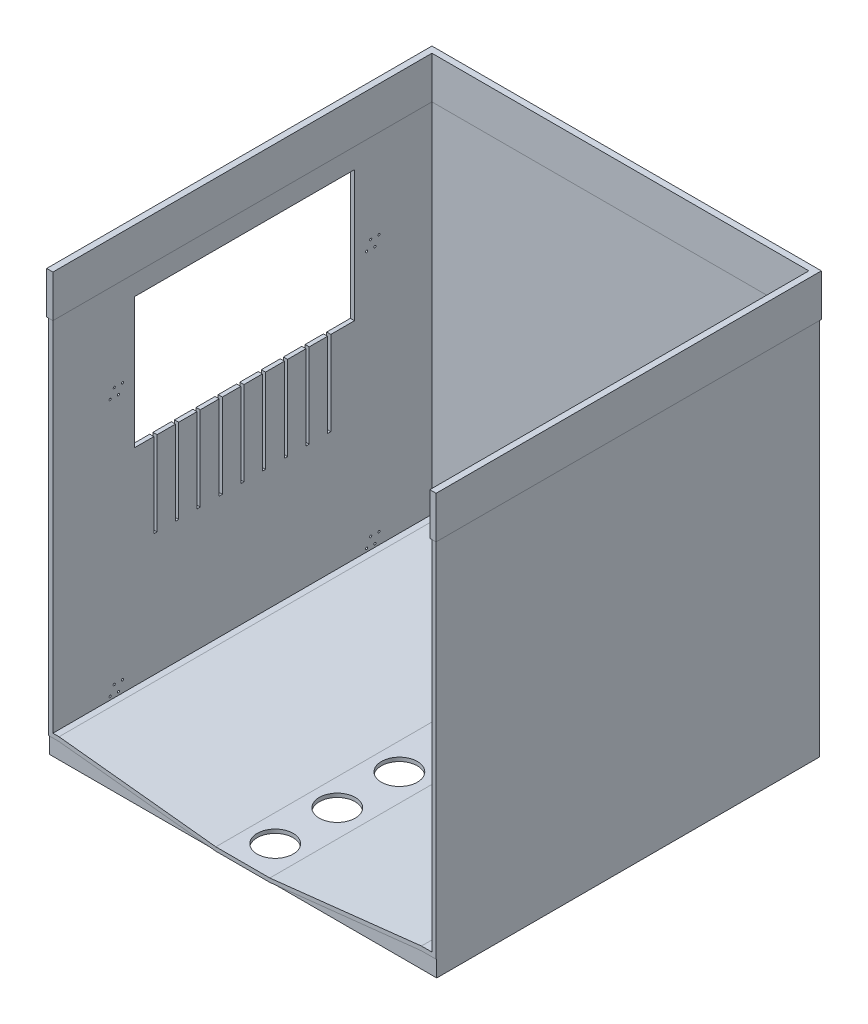
SolidWorks part; units mm, degrees
other "Markup1"
sketch "Sketch7" plane through (469.7075, 914.4, 622.6947) normal (0.575, 0.8073, 0.133) x (0.2253, 0, -0.9743)
ref_plane "Front Plane" through (0, 0, 0) normal (0, 0, 1) x (1, 0, 0)
ref_plane "Top Plane" through (0, 0, 0) normal (0, 1, 0) x (1, 0, 0)
ref_plane "Right Plane" through (0, 0, 0) normal (1, 0, 0) x (0, 0, -1)
sketch "Sketch1" plane through (0, 0, 0) normal (0, 1, 0) x (1, 0, 0)
  line L1 (-454.6925, 291.7053) -> (459.7075, 291.7053)
  line L2 (-454.6925, 291.7053) -> (-454.6925, -622.6947)
  line L3 (-454.6925, -622.6947) -> (459.7075, -622.6947)
  line L4 (459.7075, 291.7053) -> (459.7075, -622.6947)
  dimension "D1" = 914.4
  dimension "D2" = 914.4
extrude "Boss-Extrude1" add sketch "Sketch1" along normal blind 50
sketch "Sketch2" plane through (459.7075, 0, 0) normal (1, 0, 0) x (0, 0, -1)
  line L0 (291.7053, 50) -> (291.7053, 0) construction
  line L1 (-622.6947, 0) -> (291.7053, 0)
  line L2 (-622.6947, 0) -> (-622.6947, 914.4)
  line L3 (-622.6947, 914.4) -> (291.7053, 914.4)
  line L4 (291.7053, 0) -> (291.7053, 914.4)
  dimension "D1" = 914.4
  dimension "D2" = 0
extrude "Boss-Extrude2" add sketch "Sketch2" along normal blind 10
sketch "Sketch4" plane through (-454.6925, 0, 0) normal (-1, 0, 0) x (0, 0, 1)
  line L1 (-291.7053, 0) -> (622.6947, 0)
  line L2 (-291.7053, 0) -> (-291.7053, 914.4)
  line L3 (-291.7053, 914.4) -> (622.6947, 914.4)
  line L4 (622.6947, 0) -> (622.6947, 914.4)
extrude "Boss-Extrude3" add sketch "Sketch4" along normal blind 10
sketch "Sketch5" plane through (0, 0, -291.7053) normal (0, 0, -1) x (-1, 0, 0)
  line L0 (464.6925, 914.4) -> (464.6925, 0) construction
  line L1 (-469.7075, 0) -> (464.6925, 0)
  line L2 (-469.7075, 0) -> (-469.7075, 914.4)
  line L3 (-469.7075, 914.4) -> (464.6925, 914.4)
  line L4 (464.6925, 0) -> (464.6925, 914.4)
extrude "Boss-Extrude4" add sketch "Sketch5" along normal blind 10 contours L3 L4 L1 L2
sketch "Sketch6" plane through (0, 0, 622.6947) normal (0, 0, 1) x (1, 0, 0)
  line L0 (0, 0) -> (-61.619, 0)
  line L1 (-464.6925, 0) -> (469.7075, 0) construction
  line L2 (0, 0) -> (68.6447, 0)
  line L3 (68.6447, 0) -> (434.3849, 40)
  line L4 (434.3849, 40) -> (469.7075, 40)
  line L5 (469.7075, 914.4) -> (469.7075, 0) construction
  line L6 (-61.619, 0) -> (-439.8845, 40)
  line L7 (-439.8845, 40) -> (-464.6925, 40)
  line L8 (-464.6925, 0) -> (-464.6925, 914.4) construction
  line L9 (469.7075, 40) -> (469.7075, 0)
  line L10 (469.7075, 0) -> (68.6447, 0)
  line L11 (-464.6925, 40) -> (-464.6925, 0)
  line L12 (-464.6925, 0) -> (-61.619, 0)
  line L13 (459.7075, 50) -> (-454.6925, 50) construction
  line L14 (-439.8845, 50) -> (-61.619, 9.2201)
  line L15 (-454.6925, 50) -> (459.7075, 50) construction
  line L16 (-61.619, 9.2201) -> (-61.619, 0)
  line L17 (-439.8845, 50) -> (434.3849, 50)
  line L18 (434.3849, 50) -> (68.6447, 9.2201)
  line L19 (68.6447, 9.2201) -> (-61.619, 9.2201)
  line L20 (68.6447, 0) -> (68.6447, 9.2201)
  line L21 (434.3849, 40) -> (434.3849, 50)
  line M13 (-464.6925, 0) -> (469.7075, 0)
  line M14 (469.7075, 0) -> (469.7075, 914.4)
  line M17 (459.7075, 50) -> (-454.6925, 50)
  line M20 (-464.6925, 914.4) -> (-464.6925, 0)
  dimension "D1" = 10
  dimension "D2" = 10
  dimension "D3" = 35.3226
  dimension "D4" = 378.2656
  dimension "D5" = 378.2656
extrude "Cut-Extrude2" cut sketch "Sketch6" against normal through all contours L6 L7 M20 M13 | L19 L18 L14 M17 | L4 L3 M13 M14
sketch "Sketch8" plane through (0, 0, -301.7053) normal (0, 0, -1) x (-1, 0, 0)
  line L0 (-434.3849, 50) -> (-68.6447, 9.2201)
  line L1 (-68.6447, 9.2201) -> (61.619, 9.2201)
  line L2 (61.619, 9.2201) -> (439.8845, 50)
  line L3 (439.8845, 50) -> (-434.3849, 50)
extrude "Boss-Extrude5" add sketch "Sketch8" against normal blind 10
sketch "Sketch10" plane through (0, 9.2201, 0) normal (0, 1, 0) x (1, 0, 0)
  line L0 (3.5129, -622.6947) -> (2.5075, 291.7053)
  line L1 (68.6447, -622.6947) -> (-61.619, -622.6947) construction
  line L2 (459.7075, 291.7053) -> (-454.6925, 291.7053) construction
  line L3 (3.427, -544.5816) -> (3.2621, -394.5816) construction
  circle A0 centre (3.427, -544.5816) radius 43.3569
  circle A1 centre (3.2621, -394.5816) radius 43.3569
  circle A2 centre (3.0971, -244.5817) radius 43.3569
  circle A3 centre (2.9322, -94.5818) radius 43.3569
  circle A4 centre (2.7673, 55.4181) radius 43.3569
  circle A5 centre (2.6024, 205.418) radius 43.3569
  dimension "D2" = 150
  dimension "D3" = 0
  dimension "D1" = 6
extrude "Cut-Extrude3" cut sketch "Sketch10" against normal through all contours A5 | A4 | A3 | A2 | A1 | A0
sketch "Sketch11" plane through (-464.6925, 0, 0) normal (-1, 0, 0) x (0, 0, 1)
  line L0 (-301.7053, 40) -> (622.6947, 40) construction
  line L1 (-104.8553, 863.6) -> (425.8447, 863.6)
  line L2 (-104.8553, 863.6) -> (-104.8553, 548)
  line L3 (-104.8553, 548) -> (425.8447, 548)
  line L4 (425.8447, 863.6) -> (425.8447, 548)
  line L5 (-301.7053, 40) -> (-301.7053, 914.4) construction
  line L6 (622.6947, 40) -> (622.6947, 914.4) construction
  line L7 (622.6947, 914.4) -> (-301.7053, 914.4) construction
  dimension "D1" = 508
  dimension "D2" = 196.85
  dimension "D3" = 196.85
  dimension "D4" = 50.8
extrude "Cut-Extrude4" cut sketch "Sketch11" against normal blind 10
sketch "Sketch14" plane through (0, 914.4, 0) normal (0, 1, 0) x (1, 0, 0)
  line L16 (457.1675, 289.1653) -> (457.1675, -625.2347)
  line L17 (457.1675, -625.2347) -> (472.2475, -625.2347)
  line L18 (472.2475, -625.2347) -> (472.2475, 304.2453)
  line L19 (472.2475, 304.2453) -> (-467.2325, 304.2453)
  line L20 (-467.2325, 304.2453) -> (-467.2325, -625.2347)
  line L21 (-467.2325, -625.2347) -> (-452.1525, -625.2347)
  line L22 (-452.1525, -625.2347) -> (-452.1525, 289.1653)
  line L23 (-452.1525, 289.1653) -> (457.1675, 289.1653)
  line L24 (457.1675, 289.1653) -> (457.1675, -625.2347)
  line L25 (457.1675, -625.2347) -> (472.2475, -625.2347)
  line L26 (472.2475, -625.2347) -> (472.2475, 304.2453)
  line L27 (472.2475, 304.2453) -> (-467.2325, 304.2453)
  line L28 (-467.2325, 304.2453) -> (-467.2325, -625.2347)
  line L29 (-467.2325, -625.2347) -> (-452.1525, -625.2347)
  line L30 (-452.1525, -625.2347) -> (-452.1525, 289.1653)
  line L31 (-452.1525, 289.1653) -> (457.1675, 289.1653)
  dimension "D1" = 2.54
extrude "Boss-Extrude7" add sketch "Sketch14" along normal blind 101.6
sketch "Sketch16" plane through (0, 0, -301.7053) normal (0, 0, -1) x (-1, 0, 0)
  line L0 (-469.7075, 40) -> (-469.7075, 0)
  line L1 (-469.7075, 0) -> (-68.6447, 0)
  line L2 (-68.6447, 0) -> (-434.3849, 40)
  line L3 (-434.3849, 40) -> (-469.7075, 40)
  line L4 (61.619, 0) -> (439.8845, 40)
  line L5 (439.8845, 40) -> (464.6925, 40)
  line L6 (464.6925, 40) -> (464.6925, 0)
  line L7 (464.6925, 0) -> (61.619, 0)
extrude "Boss-Extrude8" add sketch "Sketch16" against normal blind 922.782
sketch "Sketch17" plane through (-464.6925, 0, 0) normal (-1, 0, 0) x (0, 0, 1)
  circle A0 centre (-164.1053, 77.7367) radius 2.5
  circle A1 centre (-144.1053, 77.7367) radius 2.5
  circle A2 centre (-134.1053, 57.7367) radius 2.5
  circle A3 centre (-154.1053, 57.7367) radius 2.5
  circle A4 centre (474.6947, 77.7367) radius 2.5
  circle A5 centre (484.6947, 57.7367) radius 2.5
  circle A6 centre (464.6947, 57.7367) radius 2.5
  circle A7 centre (454.6947, 77.7367) radius 2.5
  circle A8 centre (-164.1053, 698.1498) radius 2.5
  circle A9 centre (-144.1053, 698.1498) radius 2.5
  circle A10 centre (-134.1053, 678.1498) radius 2.5
  circle A11 centre (-154.1053, 678.1498) radius 2.5
  circle A12 centre (474.6947, 698.1498) radius 2.5
  circle A13 centre (484.6947, 678.1498) radius 2.5
  circle A14 centre (464.6947, 678.1498) radius 2.5
  circle A15 centre (454.6947, 698.1498) radius 2.5
extrude "Cut-Extrude5" cut sketch "Sketch17" against normal up to surface (10 mm away) up to face at (-454.6925, 705.8, 160.4947)
sketch "Sketch18" plane through (-464.6925, 0, 0) normal (-1, 0, 0) x (0, 0, 1)
  line L0 (-104.8553, 548) -> (425.8447, 548) construction
  line L1 (-47.7053, 548) -> (-40.0853, 548)
  line L2 (-47.7053, 548) -> (-47.7053, 344.8)
  line L3 (-47.7053, 344.8) -> (-40.0853, 344.8)
  line L4 (-40.0853, 548) -> (-40.0853, 344.8)
  line L5 (-104.8553, 863.6) -> (-104.8553, 548) construction
  line L7 (4.3647, 548) -> (11.9847, 548)
  line L8 (4.3647, 548) -> (4.3647, 344.8)
  line L9 (4.3647, 344.8) -> (11.9847, 344.8)
  line L10 (56.4347, 548) -> (56.4347, 344.8)
  line L11 (56.4347, 344.8) -> (64.0547, 344.8)
  line L12 (64.0547, 344.8) -> (64.0547, 548)
  line L13 (11.9847, 548) -> (11.9847, 344.8)
  line L14 (109.7747, 548) -> (109.7747, 344.8)
  line L15 (109.7747, 344.8) -> (117.3947, 344.8)
  line L16 (117.3947, 344.8) -> (117.3947, 548)
  line L18 (161.8447, 548) -> (161.8447, 344.8)
  line L19 (161.8447, 344.8) -> (169.4647, 344.8)
  line L20 (169.4647, 344.8) -> (169.4647, 548)
  line L22 (213.9147, 548) -> (213.9147, 344.8)
  line L23 (213.9147, 344.8) -> (221.5347, 344.8)
  line L24 (221.5347, 344.8) -> (221.5347, 548)
  line L26 (267.2547, 548) -> (267.2547, 344.8)
  line L27 (267.2547, 344.8) -> (274.8747, 344.8)
  line L28 (274.8747, 344.8) -> (274.8747, 548)
  line L29 (274.8747, 548) -> (267.2547, 548)
  line L31 (319.3247, 548) -> (326.9447, 548)
  line L32 (319.3247, 548) -> (319.3247, 344.8)
  line L33 (319.3247, 344.8) -> (326.9447, 344.8)
  line L34 (326.9447, 548) -> (326.9447, 344.8)
  line L35 (371.3947, 548) -> (379.0147, 548)
  line L36 (371.3947, 548) -> (371.3947, 344.8)
  line L37 (371.3947, 344.8) -> (379.0147, 344.8)
  line L38 (379.0147, 548) -> (379.0147, 344.8)
  line L39 (56.4347, 548) -> (64.0547, 548)
  line L40 (109.7747, 548) -> (117.3947, 548)
  line L41 (161.8447, 548) -> (169.4647, 548)
  line L42 (213.9147, 548) -> (221.5347, 548)
  dimension "D1" = 57.15
  dimension "D2" = 7.62
  dimension "D3" = 44.45
  dimension "D4" = 7.62
  dimension "D5" = 44.45
  dimension "D6" = 7.62
  dimension "D7" = 45.72
  dimension "D8" = 7.62
  dimension "D9" = 44.45
  dimension "D10" = 7.62
  dimension "D11" = 44.45
  dimension "D12" = 7.62
  dimension "D13" = 45.72
  dimension "D14" = 7.62
  dimension "D15" = 44.45
  dimension "D16" = 7.62
  dimension "D17" = 44.45
  dimension "D18" = 7.62
  dimension "D19" = 203.2
  dimension "D20" = 203.2
extrude "Cut-Extrude6" cut sketch "Sketch18" against normal up to surface (10 mm away) up to face at (-454.6925, 698.1498, -166.6053)
